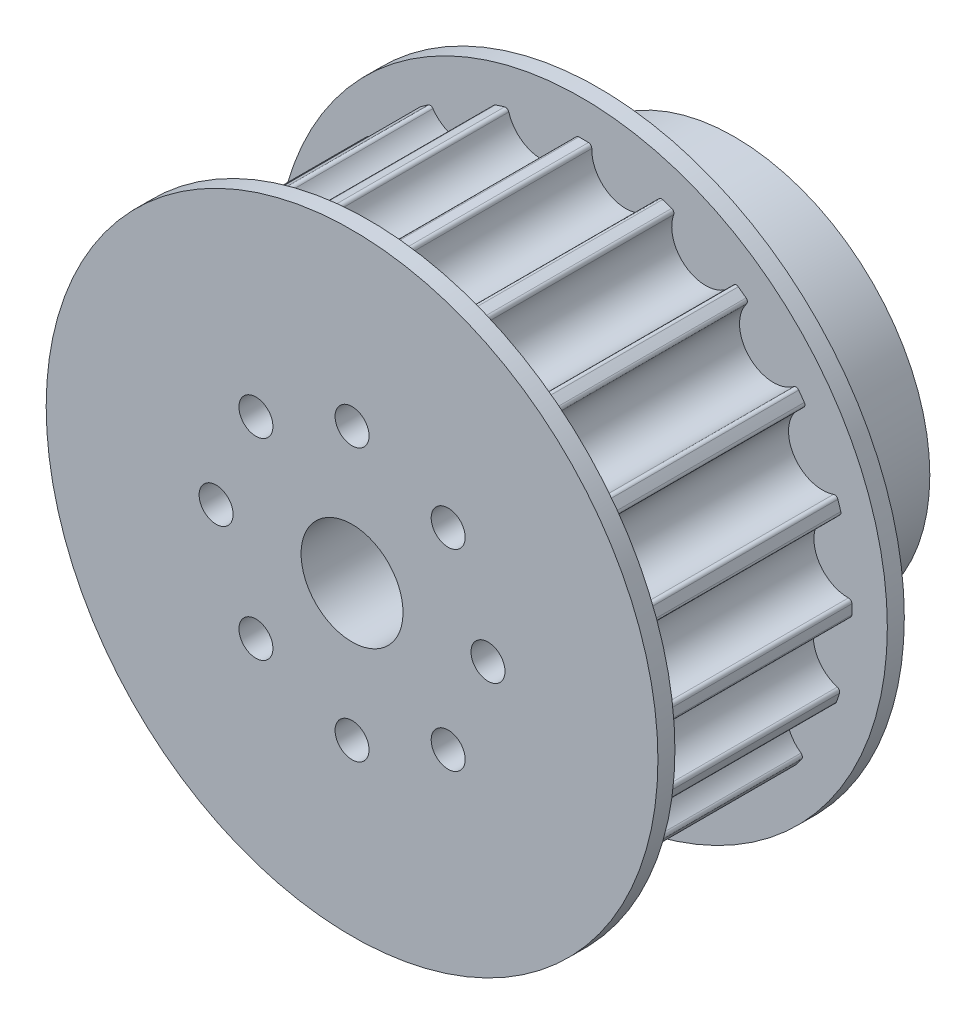
SolidWorks part; units mm, degrees
ref_plane "Plan de face" through (0, 0, 0) normal (0, 0, 1) x (1, 0, 0)
ref_plane "Plan de dessus" through (0, 0, 0) normal (0, 1, 0) x (1, 0, 0)
ref_plane "Plan de droite" through (0, 0, 0) normal (1, 0, 0) x (0, 0, -1)
sketch "Esquisse1" plane through (0, 0, 0) normal (0, 0, 1) x (1, 0, 0)
  circle A0 centre (0, 0) radius 11.5
  dimension "D1" = 23
extrude "Boss.-Extru.1" add sketch "Esquisse1" along normal blind 8
sketch "Esquisse2" plane through (0, 0, 8) normal (0, 0, 1) x (1, 0, 0)
  circle A0 centre (0, 0) radius 18
  dimension "D1" = 36
extrude "Boss.-Extru.2" add sketch "Esquisse2" along normal blind 1
sketch "Esquisse3" plane through (0, 0, 9) normal (0, 0, 1) x (1, 0, 0)
  line L0 (0.1344, 15.9144) -> (0.1091, 12.9145)
  line L1 (-4.8003, 15.1738) -> (-3.8954, 12.3135)
  arc A0 (-4.3213, 15.3171) -> (-0.3656, 15.9108) centre (-2.3534, 15.6805) ccw
  arc A1 (-4.3213, 15.3171) -> (-4.8003, 15.1738) centre (0, 0) ccw
  arc A2 (0.1344, 15.9144) -> (-0.3656, 15.9108) centre (0, 0) ccw
  arc A3 (0.1091, 12.9145) -> (-3.8954, 12.3135) centre (0, 0) ccw
  dimension "D1" = 4
  dimension "D2" = 31.83
  dimension "D5" = 0.5
  dimension "D4" = 0.5
extrude "Boss.-Extru.3" add sketch "Esquisse3" along normal blind 12.5
pattern_circular "Répétition circulaire1" count 20 over 360 about axis through (0, 0, 0) along (0, 0, 1) of "Boss.-Extru.3"
fillet "Congé1" radius 0.2 40 edges at (-14.9318, 5.5072, 15.25) (-15.245, 4.569, 15.25) (-15.9028, 0.6235, 15.25) (-15.9108, -0.3656, 15.25) (-15.3171, -4.3213, 15.25) (-15.0191, -5.2644, 15.25) (-13.2321, -8.843, 15.25) (-12.6572, -9.6479, 15.25) (-9.8518, -12.4992, 15.25) (-9.0564, -13.087, 15.25) (-5.5072, -14.9318, 15.25) (-4.569, -15.245, 15.25) (-0.6235, -15.9028, 15.25) (0.3656, -15.9108, 15.25) (5.2644, -15.0191, 15.25) (4.3213, -15.3171, 15.25) (8.843, -13.2321, 15.25) (9.6479, -12.6572, 15.25) (12.4992, -9.8518, 15.25) (13.087, -9.0564, 15.25) (15.9108, 0.3656, 15.25) (14.9318, -5.5072, 15.25) (15.245, -4.569, 15.25) (15.9028, -0.6235, 15.25) (15.3171, 4.3213, 15.25) (15.0191, 5.2644, 15.25) (13.2321, 8.843, 15.25) (12.6572, 9.6479, 15.25) (9.0564, 13.087, 15.25) (9.8518, 12.4992, 15.25) (5.5072, 14.9318, 15.25) (4.569, 15.245, 15.25) (0.6235, 15.9028, 15.25) (-4.3213, 15.3171, 15.25) (-0.3656, 15.9108, 15.25) (-5.2644, 15.0191, 15.25) (-12.4992, 9.8518, 15.25) (-13.087, 9.0564, 15.25) (-9.6479, 12.6572, 15.25) (-8.843, 13.2321, 15.25)
sketch "Esquisse7" plane through (0, 0, 9) normal (0, 0, 1) x (1, 0, 0)
  circle A0 centre (0, 0) radius 12.915
extrude "Boss.-Extru.5" add sketch "Esquisse7" along normal blind 12.5
sketch "Esquisse8" plane through (0, 0, 21.5) normal (0, 0, 1) x (1, 0, 0)
  circle A0 centre (0, 0) radius 18
  dimension "D1" = 36
extrude "Boss.-Extru.6" add sketch "Esquisse8" along normal blind 1
sketch "Esquisse9" plane through (0, 0, 22.5) normal (0, 0, 1) x (1, 0, 0)
  circle A0 centre (0, 0) radius 3
  dimension "D1" = 6
extrude "Enlèv. mat.-Extru.1" cut sketch "Esquisse9" against normal through all contours A0
sketch "Esquisse10" plane through (0, 0, 0) normal (0, 0, -1) x (-1, 0, 0)
  circle A0 centre (0, 8) radius 1
  dimension "D1" = 8
  dimension "D2" = 2
extrude "Enlèv. mat.-Extru.2" cut sketch "Esquisse10" against normal through all
pattern_circular "Répétition circulaire2" count 8 over 360 about axis through (0, 0, 0) along (0, 0, 1) of "Enlèv. mat.-Extru.2"
